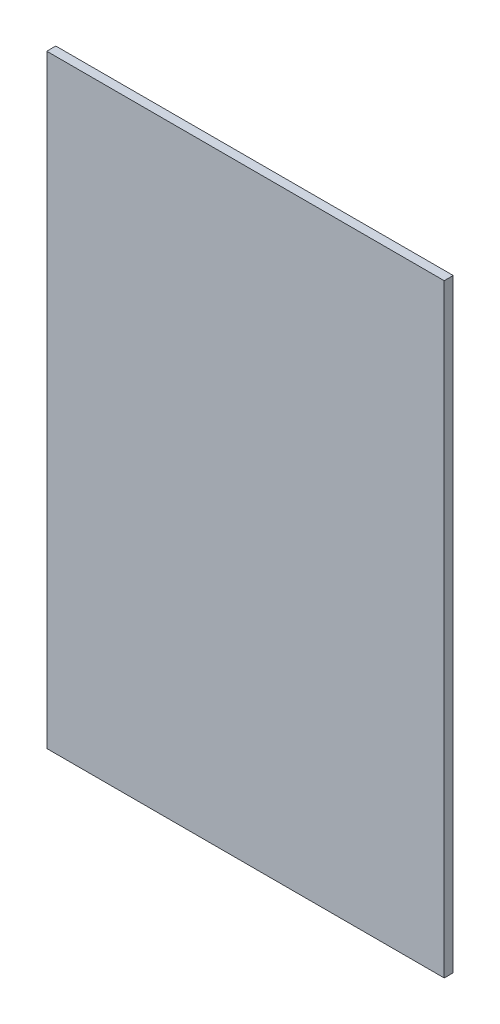
SolidWorks part; units mm, degrees
ref_plane "Спереди" through (0, 0, 0) normal (0, 0, 1) x (1, 0, 0)
ref_plane "Сверху" through (0, 0, 0) normal (0, 1, 0) x (1, 0, 0)
ref_plane "Справа" through (0, 0, 0) normal (1, 0, 0) x (0, 0, -1)
sketch "Sketch1" plane through (0, 0, 0) normal (0, 0, 1) x (1, 0, 0)
  line L6 (88.2, 130) -> (88.2, -130) construction
  line L7 (-88.2, -134) -> (88.2, -134)
  line L8 (-88.2, -134) -> (-88.2, 134)
  line L9 (-88.2, 134) -> (88.2, 134)
  line L10 (88.2, -134) -> (88.2, 134)
  line L11 (-88.2, -134) -> (88.2, 134) construction
  line L12 (-88.2, 134) -> (88.2, -134) construction
  line L13 (-88.2, -134) -> (88.2, -134) construction
  point P0 (0, 0)
extrude "Extrude1" add sketch "Sketch1" along normal blind 4
equation "\"thickness\"=4"
equation "\"D1@Extrude1\"=\"thickness\""
equation "\"pin_l\"=5"
equation "\"pin_skew\"=4"
equation "\"pin_r\"=5"
equation "\"M4_plastic_thread\"=3.8"
equation "\"M3_plastic_thread\" = 2.8"
